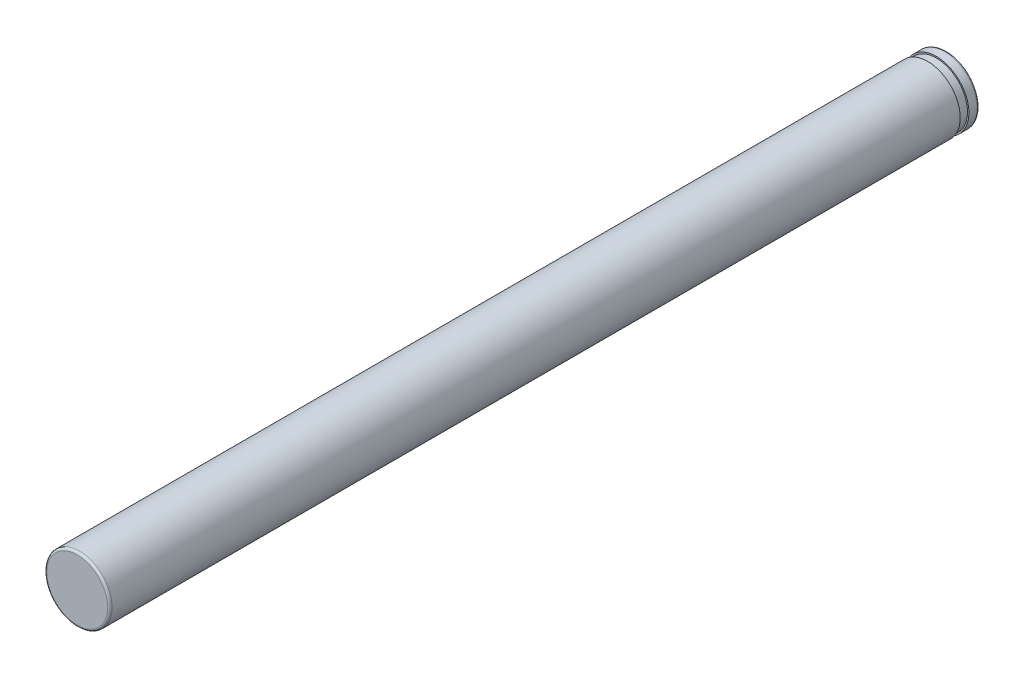
SolidWorks part; units mm, degrees
material "AISI 316 Stainless Steel Sheet (SS)"
ref_plane "Front Plane" through (0, 0, 0) normal (0, 0, 1) x (1, 0, 0)
ref_plane "Top Plane" through (0, 0, 0) normal (0, 1, 0) x (1, 0, 0)
ref_plane "Right Plane" through (0, 0, 0) normal (1, 0, 0) x (0, 0, -1)
sketch "Sketch1" plane through (0, 0, 0) normal (0, 0, 1) x (1, 0, 0)
  circle A0 centre (0, 0) radius 1.5
extrude "Boss-Extrude1" add sketch "Sketch1" along normal blind 40
fillet "Fillet1" radius 0.1 1 edges at (1.5, 0, 40)
fillet "Fillet2" radius 0.1 1 edges at (1.5, 0, 0)
sketch "Sketch2" plane through (0, 0, 0) normal (0, 1, 0) x (1, 0, 0)
  line L0 (-1.4344, -0.4756) -> (-1.4344, -0.8756)
  line L1 (-1.5826, -0.4756) -> (-1.4344, -0.4756)
  line L2 (-1.5826, -0.4756) -> (-1.5826, -0.8756)
  line L3 (-1.5826, -0.8756) -> (-1.4344, -0.8756)
  line L5 (0, 0) -> (0, -0.8756) construction
  line L6 (1.4, 0) -> (-1.4, 0) construction
  point P0 (0.0162, -0.6756)
revolve "Cut-Revolve1" cut sketch "Sketch2" angle 360 about L5
